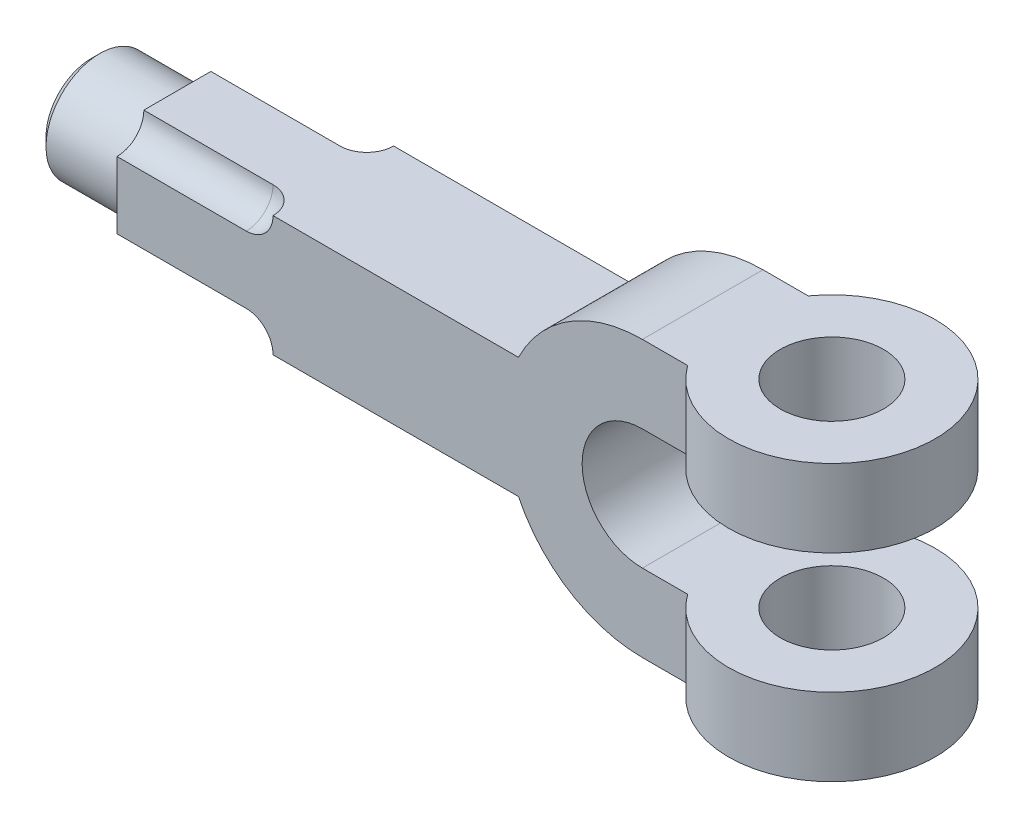
SolidWorks part; units mm, degrees
ref_plane "Front Plane" through (0, 0, 0) normal (0, 0, 1) x (1, 0, 0)
ref_plane "Top Plane" through (0, 0, 0) normal (0, 1, 0) x (1, 0, 0)
ref_plane "Right Plane" through (0, 0, 0) normal (1, 0, 0) x (0, 0, -1)
sketch "Sketch1" plane through (0, 0, 0) normal (0, 0, 1) x (1, 0, 0)
  line L0 (0, 32) -> (18, 32)
  line L1 (0, 14) -> (18, 14)
  line L2 (0, -14) -> (18, -14)
  line L3 (0, -32) -> (18, -32)
  line L4 (18, 32) -> (18, 14)
  line L5 (18, -14) -> (18, -32)
  arc A0 (0, 14) -> (0, -14) centre (0, 0) ccw
  arc A1 (0, 32) -> (0, -32) centre (0, 0) ccw
  dimension "D1" = 28
  dimension "D2" = 64
  dimension "D3" = 18
extrude "Boss-Extrude1" add sketch "Sketch1" along normal mid plane 28
sketch "Sketch2" plane through (0, 32, 0) normal (0, 1, 0) x (1, 0, 0)
  line L0 (18, -14) -> (18, 14) construction
  circle A0 centre (30, 0) radius 12
  circle A1 centre (30, 0) radius 24
  dimension "D1" = 48
  dimension "D2" = 24
extrude "Boss-Extrude2" add sketch "Sketch2" against normal blind 18
mirror "Mirror1" about plane through (0, 0, 0) normal (0, 1, 0) of "Boss-Extrude2"
ref_plane "Plane1" through (-122, 0, 0) normal (1, 0, 0) x (0, 0, -1)
sketch "Sketch3" plane through (-122, 0, 0) normal (1, 0, 0) x (0, 0, -1)
  line L1 (14, 14) -> (-14, 14)
  line L2 (14, 14) -> (14, -14)
  line L3 (14, -14) -> (-14, -14)
  line L4 (-14, 14) -> (-14, -14)
  line L5 (14, 14) -> (-14, -14) construction
  line L6 (14, -14) -> (-14, 14) construction
  point P0 (0, 0)
  dimension "D1" = 28
  dimension "D2" = 28
extrude "Boss-Extrude3" add sketch "Sketch3" along normal up to next
sketch "Sketch4" plane through (0, 0, 14) normal (0, 0, 1) x (1, 0, 0)
  line L0 (-122, 14) -> (-122, 7.78)
  line L1 (-122, -26.4) -> (-122, 26.4) construction
  line L2 (-122, 7.78) -> (-92, 7.78)
  line L3 (-28.775, 14) -> (-122, 14) construction
  line L4 (-122, 14) -> (-85.78, 14)
  arc A0 (-92, 7.78) -> (-85.78, 14) centre (-92, 14) ccw
  dimension "D1" = 6.22
  dimension "D2" = 0
  dimension "D3" = 30
  dimension "D4" = 36.22
revolve "Cut-Revolve1" cut sketch "Sketch4" angle 360 about axis through (500000, 14, 14) along (-1, 0, 0)
mirror "Mirror2" about plane through (0, 0, 0) normal (0, 0, 1) of "Cut-Revolve1"
mirror "Mirror3" about plane through (0, 0, 0) normal (0, 1, 0) of "Cut-Revolve1", "Mirror2"
sketch "Sketch5" plane through (-122, 0, 0) normal (-1, 0, 0) x (0, 0, 1)
  circle A0 centre (0, 0) radius 12.5
  dimension "D1" = 25
extrude "Boss-Extrude4" add sketch "Sketch5" along normal blind 20
chamfer "Chamfer1" distance 2 angle 45 1 edges at (-142, 0, 12.5)
